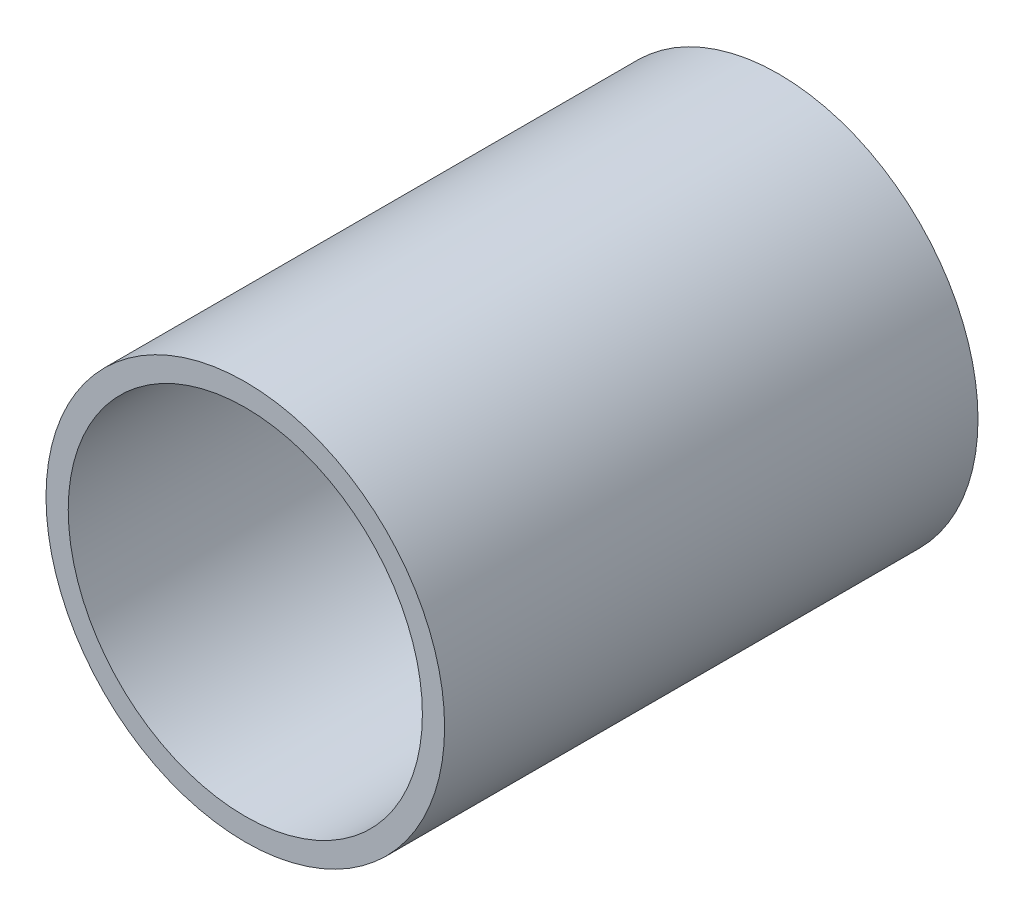
SolidWorks part; units mm, degrees
material "Acrylic (Medium-high impact)"
ref_plane "Front Plane" through (0, 0, 0) normal (0, 0, 1) x (1, 0, 0)
ref_plane "Top Plane" through (0, 0, 0) normal (0, 1, 0) x (1, 0, 0)
ref_plane "Right Plane" through (0, 0, 0) normal (1, 0, 0) x (0, 0, -1)
sketch "Sketch1" plane through (0, 0, 0) normal (0, 0, 1) x (1, 0, 0)
  circle A0 centre (0, 0) radius 56.945
  circle A1 centre (0, 0) radius 50.595
  dimension "D1" = 101.19
  dimension "D2" = 6.35
extrude "Boss-Extrude1" add sketch "Sketch1" along normal blind 152.4
